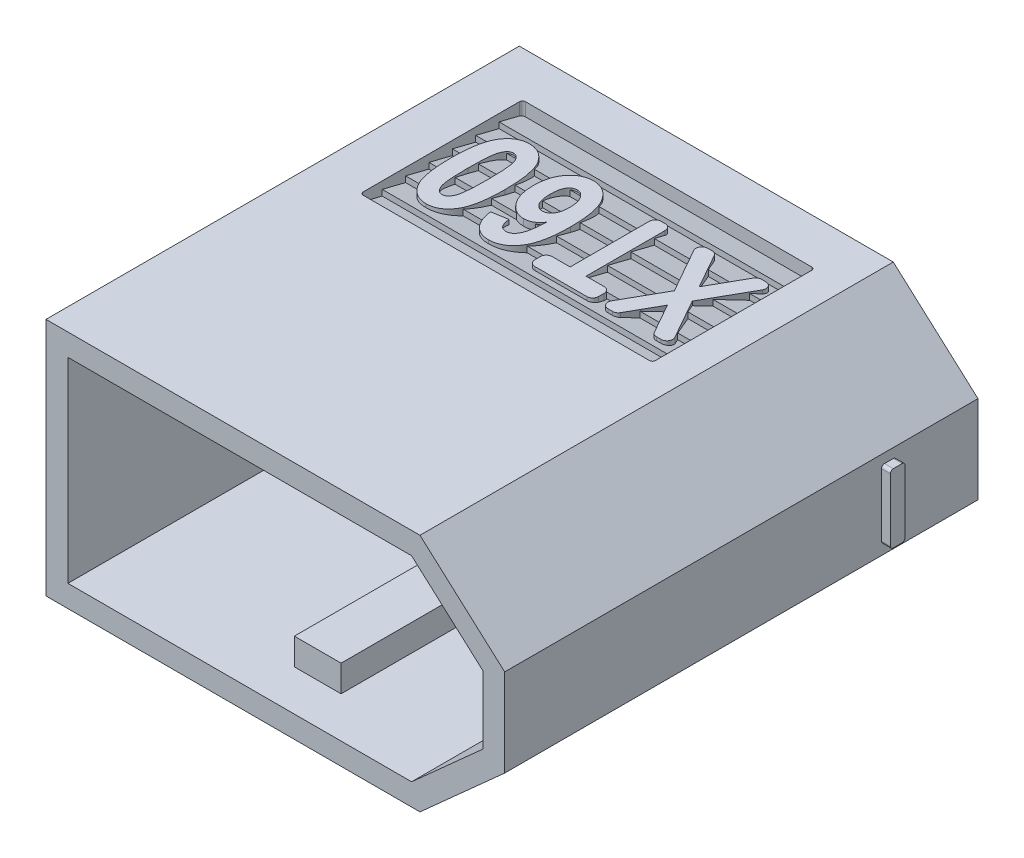
SolidWorks part; units mm, degrees
material "Nylon 101"
ref_plane "Plano frontal" through (0, 0, 0) normal (0, 0, 1) x (1, 0, 0)
ref_plane "Plano superior" through (0, 0, 0) normal (0, 1, 0) x (1, 0, 0)
ref_plane "Plano direito" through (0, 0, 0) normal (1, 0, 0) x (0, 0, -1)
sketch "Esboço1" plane through (0, 0, 0) normal (0, 0, 1) x (1, 0, 0)
  line L0 (0, 0) -> (12.8, 0)
  line L1 (12.8, 0) -> (15.7, 2.6)
  line L2 (15.7, 2.6) -> (15.7, 5.6)
  line L3 (15.7, 5.6) -> (12.8, 8.2)
  line L4 (12.8, 8.2) -> (0, 8.2)
  line L5 (0, 8.2) -> (0, 0)
  dimension "D1" = 12.8
  dimension "D2" = 3
  dimension "D3" = 15.7
  dimension "D4" = 8.2
extrude "Ressalto-extrusão1" add sketch "Esboço1" along normal blind 16.2
sketch "Esboço2" plane through (0, 0, 16.2) normal (0, 0, 1) x (1, 0, 0)
  line L0 (0.75, 7.45) -> (0.75, 0.75)
  line L1 (0.75, 0.75) -> (12.513, 0.75)
  line L2 (12.513, 0.75) -> (14.95, 2.9349)
  line L3 (14.95, 2.9349) -> (14.95, 5.2651)
  line L4 (14.95, 5.2651) -> (12.513, 7.45)
  line L5 (12.513, 7.45) -> (0.75, 7.45)
  line L6 (0, 8.2) -> (0, 0)
  line L7 (0, 0) -> (12.8, 0)
  line L8 (12.8, 0) -> (15.7, 2.6)
  line L9 (15.7, 2.6) -> (15.7, 5.6)
  line L10 (15.7, 5.6) -> (12.8, 8.2)
  line L11 (12.8, 8.2) -> (0, 8.2)
  line L12 (0, 8.2) -> (0, 0) construction
  line L13 (0, 0) -> (12.8, 0) construction
  line L14 (12.8, 0) -> (15.7, 2.6) construction
  line L15 (15.7, 2.6) -> (15.7, 5.6) construction
  line L16 (15.7, 5.6) -> (12.8, 8.2) construction
  line L17 (12.8, 8.2) -> (0, 8.2) construction
  dimension "D1" = 0
  dimension "D2" = 0.75
extrude "Corte-extrusão1" cut sketch "Esboço2" against normal blind 9.4
sketch "Esboço3" plane through (0, 0, 6.8) normal (0, 0, 1) x (1, 0, 0)
  line L1 (7.1, 1.66) -> (8.7, 1.66)
  line L2 (7.1, 1.66) -> (7.1, 0.75)
  line L3 (7.1, 0.75) -> (8.7, 0.75)
  line L4 (8.7, 1.66) -> (8.7, 0.75)
  line L7 (0.75, 0.75) -> (12.513, 0.75) construction
  line L8 (0, 0) -> (12.8, 0) construction
  line L9 (0, 8.2) -> (0, 0) construction
  dimension "D1" = 1.6
  dimension "D2" = 1.66
  dimension "D3" = 8.7
extrude "Ressalto-extrusão2" add sketch "Esboço3" along normal blind 8
sketch "Esboço4" plane through (0, 0, 6.8) normal (0, 0, 1) x (1, 0, 0)
  line L0 (12.513, 7.45) -> (0.75, 7.45) construction
  line L1 (8.7, 1.75) -> (7.1, 1.75)
  line L2 (8.7, 1.75) -> (8.7, 6.45)
  line L3 (8.7, 6.45) -> (7.1, 6.45)
  line L4 (7.1, 1.75) -> (7.1, 6.45)
  line L5 (0.75, 0.75) -> (7.1, 0.75) construction
  line L7 (7.1, 1.66) -> (7.1, 0.75) construction
  line L8 (8.7, 0.75) -> (8.7, 1.66) construction
  dimension "D1" = 1
  dimension "D2" = 1
extrude "Corte-extrusão2" cut sketch "Esboço4" against normal blind 1.5
sketch "Esboço5" plane through (0, 0, 0) normal (0, 0, -1) x (-1, 0, 0)
  line L0 (-15.7, 2.6) -> (-15.7, 5.6) construction
  line L3 (0, 8.2) -> (0, 0) construction
  circle A0 centre (-11.35, 4.1) radius 3
  circle A1 centre (-4.25, 4.1) radius 3
  point P6 (-15.7, 4.1)
  point P9 (-15.7, 4.1)
  dimension "D1" = 6
  dimension "D3" = 4.25
  dimension "D2" = 4.35
extrude "Corte-extrusão3" cut sketch "Esboço5" against normal blind 2
sketch "Esboço6" plane through (0, 0, 2) normal (0, 0, -1) x (-1, 0, 0)
  line L0 (-15.7, 2.6) -> (-15.7, 5.6) construction
  line L3 (0, 8.2) -> (0, 0) construction
  circle A0 centre (-11.35, 4.1) radius 2.15
  circle A2 centre (-4.25, 4.1) radius 2.15
  point P4 (-15.7, 4.1)
  dimension "D1" = 4.3
  dimension "D2" = 6.5
  dimension "D3" = 6.4
extrude "Corte-extrusão4" cut sketch "Esboço6" against normal through all
sketch "Esboço7" plane through (0, 0, 0) normal (-1, 0, 0) x (0, 0, 1)
  line L0 (2.8, 4.35) -> (2.05, 4.35)
  line L1 (4.25, 4.35) -> (3.5, 4.35)
  line L2 (4.35, 4.25) -> (4.35, 3.95)
  line L3 (4.25, 3.85) -> (3.5, 3.85)
  line L4 (1.95, 4.25) -> (1.95, 3.95)
  line L5 (3.3, 5.3) -> (3, 5.3)
  line L6 (3.4, 5.2) -> (3.4, 4.45)
  line L7 (3.3, 2.9) -> (3, 2.9)
  line L8 (2.9, 5.2) -> (2.9, 4.45)
  line L9 (2.8, 3.85) -> (2.05, 3.85)
  line L10 (3.4, 3.75) -> (3.4, 3)
  line L11 (2.9, 3.75) -> (2.9, 3)
  line L12 (0, 8.2) -> (0, 0) construction
  arc A0 (3, 2.9) -> (2.9, 3) centre (3, 3) cw
  arc A1 (3.3, 5.3) -> (3.4, 5.2) centre (3.3, 5.2) cw
  arc A2 (3, 5.3) -> (2.9, 5.2) centre (3, 5.2) ccw
  arc A3 (2.05, 4.35) -> (1.95, 4.25) centre (2.05, 4.25) ccw
  arc A4 (2.05, 3.85) -> (1.95, 3.95) centre (2.05, 3.95) cw
  arc A5 (2.8, 3.85) -> (2.9, 3.75) centre (2.8, 3.75) cw
  arc A6 (2.8, 4.35) -> (2.9, 4.45) centre (2.8, 4.45) ccw
  arc A7 (3.5, 3.85) -> (3.4, 3.75) centre (3.5, 3.75) ccw
  arc A8 (3.4, 3) -> (3.3, 2.9) centre (3.3, 3) cw
  arc A9 (4.35, 3.95) -> (4.25, 3.85) centre (4.25, 3.95) cw
  arc A10 (4.25, 4.35) -> (4.35, 4.25) centre (4.25, 4.25) cw
  arc A11 (3.5, 4.35) -> (3.4, 4.45) centre (3.5, 4.45) cw
  point P12 (1.95, 4.1)
  point P15 (0, 4.1)
  point P28 (2.9, 3.85)
  point P33 (3.4, 3.85)
  point P38 (4.35, 3.85)
  point P41 (4.35, 4.35)
  dimension "D4" = 0.1
  dimension "D1" = 2.4
  dimension "D2" = 0.5
  dimension "D3" = 4.35
extrude "Ressalto-extrusão3" add sketch "Esboço7" along normal blind 0.3
sketch "Esboço8" plane through (15.7, 0, 0) normal (1, 0, 0) x (0, 0, -1)
  line L0 (0, 2.6) -> (0, 5.6) construction
  line L1 (-3.2, 2.925) -> (-2.9, 2.925)
  line L2 (-3.3, 3.025) -> (-3.3, 5.175)
  line L3 (-3.2, 5.275) -> (-2.9, 5.275)
  line L4 (-2.8, 3.025) -> (-2.8, 5.175)
  arc A0 (-3.3, 5.175) -> (-3.2, 5.275) centre (-3.2, 5.175) cw
  arc A1 (-2.9, 5.275) -> (-2.8, 5.175) centre (-2.9, 5.175) cw
  arc A2 (-3.2, 2.925) -> (-3.3, 3.025) centre (-3.2, 3.025) cw
  arc A3 (-2.9, 2.925) -> (-2.8, 3.025) centre (-2.9, 3.025) ccw
  point P4 (-2.8, 4.1)
  point P7 (0, 4.1)
  point P10 (-3.3, 5.275)
  point P13 (-2.8, 5.275)
  point P18 (-2.8, 2.925)
  dimension "D4" = 0.1
  dimension "D1" = 2.35
  dimension "D2" = 0.5
  dimension "D3" = 3.3
extrude "Ressalto-extrusão4" add sketch "Esboço8" along normal blind 0.3
sketch "Esboço9" plane through (0, 0, 0) normal (0, -1, 0) x (1, 0, 0)
  line L0 (12.8, 16.2) -> (12.8, 0) construction
  line L1 (1.75, 7.0931) -> (11.55, 7.0931)
  line L2 (1.65, 6.9931) -> (1.65, 1.6431)
  line L3 (1.75, 1.5431) -> (11.55, 1.5431)
  line L4 (11.65, 6.9931) -> (11.65, 1.6431)
  arc A0 (1.65, 1.6431) -> (1.75, 1.5431) centre (1.75, 1.6431) ccw
  arc A1 (11.55, 1.5431) -> (11.65, 1.6431) centre (11.55, 1.6431) ccw
  arc A2 (11.55, 7.0931) -> (11.65, 6.9931) centre (11.55, 6.9931) cw
  arc A3 (1.75, 7.0931) -> (1.65, 6.9931) centre (1.75, 6.9931) ccw
  dimension "D1" = 0.1
  dimension "D2" = 1.15
  dimension "D3" = 10
  dimension "D4" = 5.55
extrude "Corte-extrusão5" cut sketch "Esboço9" against normal blind 0.75
sketch "Esboço10" plane through (1.65, 0, 0) normal (1, 0, 0) x (0, 0, -1)
  line L0 (-6.8, 0.75) -> (-1.6431, 0.75) construction
  line L1 (-1.5431, 0.75) -> (-1.5431, 0) construction
  line L2 (-3.1431, 0.25) -> (-2.3431, 0.45)
  line L3 (-2.3431, 0.45) -> (-2.3431, 0.25)
  line L5 (-3.1431, 0.45) -> (-3.1431, 0.25)
  line L6 (-2.3431, 0.45) -> (-2.3431, 0.25)
  line L7 (-3.9431, 0.25) -> (-3.1431, 0.45)
  line L8 (-3.9431, 0.45) -> (-3.9431, 0.25)
  line L9 (-4.7431, 0.25) -> (-3.9431, 0.45)
  line L10 (-4.7431, 0.45) -> (-4.7431, 0.25)
  line L11 (-5.5431, 0.25) -> (-4.7431, 0.45)
  line L12 (-5.5431, 0.45) -> (-5.5431, 0.25)
  line L13 (-6.3431, 0.25) -> (-5.5431, 0.45)
  line L14 (-6.3431, 0.45) -> (-6.3431, 0.25)
  line L15 (-7.1431, 0.25) -> (-6.3431, 0.45)
  line L16 (-7.1431, 0.45) -> (-7.1431, 0.25)
  line L17 (-7.1431, 0.45) -> (-7.1431, 0.75)
  line L19 (-2.3431, 0.25) -> (-1.5431, 0.45)
  line L20 (-7.1431, 0.75) -> (-1.5431, 0.75)
  line L21 (-1.5431, 0.45) -> (-1.5431, 0.75)
  line L31 (-2.3431, 0.25) -> (-1.5431, 0.45)
  dimension "D1" = 0.8
  dimension "D2" = 0.2
  dimension "D3" = 0.3
  dimension "D4" = 7
extrude "Ressalto-extrusão7" add sketch "Esboço10" along normal up to surface (10 mm away) up to face at (11.65, 0.45, 4.8145)
ref_plane "Plano1" through (0, 4.1, 0) normal (0, 1, 0) x (1, 0, 0)
mirror "Espelhar1" about plane through (0, 4.1, 0) normal (0, 1, 0) of "Corte-extrusão5", "Ressalto-extrusão7"
ref_plane "Plano2" through (0, 0.5, 0) normal (0, -1, 0) x (-1, 0, 0)
sketch "Esboço11" plane through (0, 0.5, 0) normal (0, -1, 0) x (-1, 0, 0)
  line L1 (-2.131, -7.0931) -> (-2.131, -1.5431) construction
  line L2 (-11.55, -7.0931) -> (-1.75, -7.0931) construction
  line L3 (-11.55, -1.5431) -> (-1.75, -1.5431) construction
  line L4 (-0.85, -6.1831) -> (-0.85, -2.4531) construction
  line L5 (-0.85, -2.4531) -> (-11.65, -2.4531) construction
  line L8 (-11.65, -3.1431) -> (-11.65, -2.3431) construction
  line L10 (-1.65, -6.9931) -> (-1.65, -1.6431) construction
  text T0 "<b><i>TGY</i></b>" font "Calibri" height in points 14
  point P8 (-0.85, -4.3181)
  point P9 (-2.131, -4.3181)
  dimension "D2" = 0.8
  dimension "D1" = 3.73
extrude "Ressalto-extrusão8" add sketch "Esboço11" along normal blind 0.3
ref_plane "Plano3" through (0, 7.7, 0) normal (0, 1, 0) x (1, 0, 0)
sketch "Esboço12" plane through (0, 7.7, 0) normal (0, 1, 0) x (1, 0, 0)
  line L0 (11.0942, -7.0931) -> (11.0942, -1.5431) construction
  line L1 (11.55, -7.0931) -> (1.75, -7.0931) construction
  line L3 (11.3535, -6.0681) -> (11.3535, -2.5681) construction
  line L6 (11.3535, -2.5681) -> (1.9746, -2.5681) construction
  line L7 (11.185, -2.8665) -> (10.3201, -4.3984)
  line L8 (10.3201, -4.3984) -> (11.0942, -5.7698)
  line L9 (10.92, -6.0681) -> (10.7649, -6.0681)
  line L10 (10.5908, -5.9665) -> (10.0126, -4.9431)
  line L11 (10.0126, -4.9431) -> (9.435, -5.9664)
  line L12 (9.2609, -6.0681) -> (9.1051, -6.0681)
  line L13 (8.931, -5.7698) -> (9.705, -4.3984)
  line L14 (9.705, -4.3984) -> (8.8401, -2.8665)
  line L15 (9.0143, -2.5681) -> (9.1699, -2.5681)
  line L16 (9.3441, -2.6698) -> (10.0126, -3.8543)
  line L17 (10.0126, -3.8543) -> (10.6817, -2.6698)
  line L18 (10.8559, -2.5681) -> (11.0109, -2.5681)
  line L19 (7.7626, -2.7681) -> (7.7626, -5.4772)
  line L20 (7.7626, -5.4772) -> (8.3808, -5.4772)
  line L21 (8.5808, -5.6772) -> (8.5808, -5.8681)
  line L22 (8.3808, -6.0681) -> (6.5989, -6.0681)
  line L23 (6.3989, -5.8681) -> (6.3989, -5.6772)
  line L24 (6.5989, -5.4772) -> (7.2171, -5.4772)
  line L25 (7.2171, -5.4772) -> (7.2171, -2.7681)
  line L26 (7.4171, -2.5681) -> (7.5626, -2.5681)
  line L27 (4.2171, -5.2045) -> (4.7626, -5.1136)
  line L28 (11.55, -1.5431) -> (1.75, -1.5431) construction
  arc A0 (7.2171, -2.7681) -> (7.4171, -2.5681) centre (7.4171, -2.7681) cw
  arc A1 (7.7626, -2.7681) -> (7.5626, -2.5681) centre (7.5626, -2.7681) ccw
  arc A2 (6.3989, -5.6772) -> (6.5989, -5.4772) centre (6.5989, -5.6772) cw
  arc A3 (6.5989, -6.0681) -> (6.3989, -5.8681) centre (6.5989, -5.8681) cw
  arc A4 (8.5808, -5.8681) -> (8.3808, -6.0681) centre (8.3808, -5.8681) cw
  arc A5 (8.3808, -5.4772) -> (8.5808, -5.6772) centre (8.3808, -5.6772) cw
  arc A6 (11.185, -2.8665) -> (11.0109, -2.5681) centre (11.0109, -2.7681) ccw
  arc A7 (10.6817, -2.6698) -> (10.8559, -2.5681) centre (10.8559, -2.7681) cw
  arc A8 (9.1699, -2.5681) -> (9.3441, -2.6698) centre (9.1699, -2.7681) cw
  arc A9 (8.8401, -2.8665) -> (9.0143, -2.5681) centre (9.0143, -2.7681) cw
  arc A10 (9.1051, -6.0681) -> (8.931, -5.7698) centre (9.1051, -5.8681) cw
  arc A11 (9.435, -5.9664) -> (9.2609, -6.0681) centre (9.2609, -5.8681) cw
  arc A12 (10.7649, -6.0681) -> (10.5908, -5.9665) centre (10.7649, -5.8681) cw
  arc A13 (11.0942, -5.7698) -> (10.92, -6.0681) centre (10.92, -5.8681) cw
  spline S0 degree 3 poles (4.7626, -5.1136) (4.7682, -5.1739) (4.7813, -5.2594) (4.8192, -5.3612) (4.8534, -5.4198) (4.8944, -5.4666) (4.9618, -5.511) (5.022, -5.5233) (5.0623, -5.5227) knots 0 0 0 0 0.323351 0.457032 0.575726 0.682828 0.785622 1 1 1 1
  spline S1 degree 3 poles (5.0623, -5.5227) (5.09, -5.5233) (5.1312, -5.5165) (5.1832, -5.4965) (5.2201, -5.4751) (5.2548, -5.4474) (5.2873, -5.4137) (5.3188, -5.3744) (5.3485, -5.328) (5.3759, -5.2719) (5.4005, -5.2044) (5.4208, -5.1242) (5.4414, -5.0325) (5.4567, -4.9277) (5.4769, -4.7639) (5.4853, -4.6343) (5.4898, -4.544) knots 0 0 0 0 0.071106 0.106432 0.143035 0.180361 0.220458 0.263402 0.309744 0.362096 0.423824 0.494518 0.575001 0.665718 0.767055 1 1 1 1
  spline S2 degree 3 poles (5.4898, -4.544) (5.4583, -4.5903) (5.407, -4.6546) (5.3276, -4.7255) (5.2671, -4.7681) (5.2028, -4.8002) (5.1126, -4.8326) (5.0401, -4.8399) (4.992, -4.8409) knots 0 0 0 0 0.277998 0.405178 0.526602 0.643637 0.760549 1 1 1 1
  spline S3 degree 3 poles (4.992, -4.8409) (4.9384, -4.84) (4.8576, -4.8324) (4.7559, -4.798) (4.6823, -4.7636) (4.6106, -4.7202) (4.5426, -4.6656) (4.4769, -4.602) (4.4148, -4.529) (4.3577, -4.4481) (4.3074, -4.36) (4.2661, -4.2652) (4.2305, -4.1646) (4.205, -4.0571) (4.1787, -3.9021) (4.1709, -3.7817) (4.1717, -3.6995) knots 0 0 0 0 0.103373 0.154207 0.205955 0.259297 0.315055 0.373347 0.435039 0.499095 0.563542 0.6298 0.697776 0.768574 0.842016 1 1 1 1
  spline S4 degree 3 poles (4.1717, -3.6995) (4.1719, -3.6124) (4.1791, -3.4851) (4.2059, -3.3214) (4.2344, -3.2096) (4.2696, -3.1044) (4.3147, -3.0075) (4.3663, -2.9169) (4.427, -2.8357) (4.4929, -2.7625) (4.5632, -2.698) (4.638, -2.6441) (4.7161, -2.5992) (4.7984, -2.5649) (4.9149, -2.5326) (5.0059, -2.5223) (5.0673, -2.5227) knots 0 0 0 0 0.157847 0.230497 0.300424 0.366636 0.431332 0.493809 0.555163 0.614703 0.672107 0.727719 0.78152 0.834986 0.88891 1 1 1 1
  spline S5 degree 3 poles (5.0673, -2.5227) (5.1348, -2.5224) (5.235, -2.5352) (5.3621, -2.5775) (5.4516, -2.6225) (5.5367, -2.6804) (5.6167, -2.7511) (5.6923, -2.8344) (5.764, -2.9301) (5.8292, -3.0408) (5.8839, -3.1688) (5.9316, -3.3125) (5.969, -3.4733) (5.9997, -3.6502) (6.0283, -3.9192) (6.0353, -4.1298) (6.0353, -4.2755) knots 0 0 0 0 0.090693 0.134685 0.17953 0.224913 0.272738 0.32276 0.375986 0.433204 0.49507 0.562819 0.636478 0.716918 0.804031 1 1 1 1
  spline S6 degree 3 poles (6.0353, -4.2755) (6.0353, -4.4236) (6.0286, -4.6379) (5.9972, -4.9112) (5.9666, -5.0917) (5.9263, -5.2555) (5.8779, -5.4031) (5.8201, -5.5343) (5.7518, -5.6479) (5.6774, -5.7469) (5.5976, -5.8325) (5.5132, -5.906) (5.4224, -5.9645) (5.3276, -6.0115) (5.1918, -6.0556) (5.0843, -6.0686) (5.0119, -6.0681) knots 0 0 0 0 0.192658 0.278521 0.357597 0.430563 0.497753 0.559502 0.616537 0.669747 0.720292 0.768555 0.814847 0.860431 0.905809 1 1 1 1
  spline S7 degree 3 poles (5.0119, -6.0681) (4.9619, -6.0679) (4.888, -6.0616) (4.793, -6.0396) (4.7258, -6.0161) (4.6619, -5.9851) (4.6002, -5.9489) (4.5418, -5.9054) (4.4872, -5.8546) (4.4355, -5.7981) (4.3903, -5.7331) (4.3488, -5.6621) (4.3131, -5.5835) (4.2805, -5.4988) (4.2454, -5.3724) (4.226, -5.2732) (4.2171, -5.2045) knots 0 0 0 0 0.115543 0.170649 0.225187 0.279791 0.334526 0.390474 0.447811 0.50673 0.567186 0.630471 0.696846 0.766493 0.839959 1 1 1 1
  spline S8 degree 3 poles (5.4444, -3.7215) (5.4434, -3.6718) (5.4418, -3.5989) (5.429, -3.5058) (5.4165, -3.4425) (5.399, -3.3843) (5.3797, -3.33) (5.3555, -3.2808) (5.3274, -3.2367) (5.298, -3.1971) (5.2668, -3.1628) (5.2343, -3.1343) (5.2019, -3.1095) (5.1674, -3.0908) (5.1199, -3.0739) (5.0828, -3.0683) (5.058, -3.0681) knots 0 0 0 0 0.178482 0.260709 0.336948 0.409468 0.478213 0.543503 0.605673 0.665087 0.720356 0.771459 0.82001 0.866345 0.91145 1 1 1 1
  spline S9 degree 3 poles (5.058, -3.0681) (5.0113, -3.0673) (4.9398, -3.0858) (4.8626, -3.147) (4.82, -3.1972) (4.7904, -3.2464) (4.7705, -3.2897) (4.7544, -3.3389) (4.7402, -3.3931) (4.7296, -3.4532) (4.7205, -3.5442) (4.7163, -3.6154) (4.7171, -3.6647) knots 0 0 0 0 0.182718 0.277312 0.381921 0.439334 0.501577 0.568146 0.641921 0.72105 0.806868 1 1 1 1
  spline S10 degree 3 poles (4.7171, -3.6647) (4.717, -3.7159) (4.7193, -3.7901) (4.7313, -3.8847) (4.7423, -3.9476) (4.7573, -4.005) (4.7747, -4.0573) (4.7959, -4.1039) (4.8285, -4.1562) (4.8734, -4.2114) (4.9574, -4.2751) (5.0328, -4.2967) (5.0829, -4.2954) knots 0 0 0 0 0.189208 0.273855 0.352112 0.425324 0.492836 0.555472 0.613995 0.720194 0.816437 1 1 1 1
  spline S11 degree 3 poles (5.0829, -4.2954) (5.1315, -4.2955) (5.2057, -4.2763) (5.2877, -4.2147) (5.333, -4.163) (5.3652, -4.1135) (5.3866, -4.0705) (5.4042, -4.0231) (5.4192, -3.9714) (5.4302, -3.915) (5.4422, -3.8316) (5.4445, -3.7663) (5.4444, -3.7215) knots 0 0 0 0 0.192976 0.293261 0.403879 0.464413 0.527516 0.593907 0.665362 0.741186 0.821937 1 1 1 1
  spline S12 degree 3 poles (2.8776, -6.0681) (2.8107, -6.0678) (2.7113, -6.0563) (2.586, -6.0147) (2.4983, -5.9711) (2.4159, -5.915) (2.3386, -5.8466) (2.2662, -5.766) (2.1985, -5.6725) (2.1376, -5.5631) (2.0855, -5.436) (2.0419, -5.2906) (2.0063, -5.1269) (1.978, -4.9448) (1.9513, -4.6654) (1.9446, -4.4461) (1.9444, -4.294) knots 0 0 0 0 0.08972 0.132871 0.17644 0.220536 0.26618 0.314488 0.365396 0.420661 0.481834 0.549191 0.623951 0.706175 0.796104 1 1 1 1
  spline S13 degree 3 poles (1.9444, -4.294) (1.9446, -4.1424) (1.9512, -3.9238) (1.9781, -3.6451) (2.0061, -3.4634) (2.0421, -3.2998) (2.0852, -3.1545) (2.1378, -3.0275) (2.1984, -2.9183) (2.2663, -2.8251) (2.3378, -2.744) (2.4152, -2.6758) (2.4975, -2.6199) (2.5847, -2.5759) (2.7095, -2.5348) (2.8083, -2.5226) (2.8748, -2.5227) knots 0 0 0 0 0.203744 0.29357 0.37599 0.450617 0.518438 0.579462 0.634858 0.685888 0.734097 0.77985 0.824051 0.867439 0.910692 1 1 1 1
  spline S14 degree 3 poles (2.8748, -2.5227) (2.9415, -2.5237) (3.0413, -2.5333) (3.1662, -2.5756) (3.2543, -2.618) (3.3363, -2.6745) (3.4139, -2.742) (3.4862, -2.8219) (3.5413, -2.8978) (3.5827, -2.965) (3.6116, -3.0212) (3.6385, -3.082) (3.6644, -3.1471) (3.6866, -3.2179) (3.708, -3.2929) (3.7271, -3.3725) (3.744, -3.4569) (3.76, -3.5458) (3.7721, -3.64) (3.784, -3.7384) (3.792, -3.842) (3.7994, -3.9499) (3.8057, -4.1036) (3.809, -4.221) (3.808, -4.3011) knots 0 0 0 0 0.089418 0.132451 0.175762 0.219738 0.26505 0.312991 0.363505 0.390209 0.418376 0.447842 0.479108 0.512034 0.546898 0.583358 0.621467 0.661946 0.704107 0.748387 0.794432 0.842956 0.893008 1 1 1 1
  spline S15 degree 3 poles (3.808, -4.3011) (3.8078, -4.4522) (3.8011, -4.6701) (3.7744, -4.9476) (3.7461, -5.1285) (3.7104, -5.2915) (3.6671, -5.4365) (3.6147, -5.5633) (3.554, -5.6725) (3.4861, -5.7657) (3.4146, -5.8468) (3.3372, -5.915) (3.255, -5.9709) (3.1677, -6.0149) (3.0429, -6.056) (2.9441, -6.0682) (2.8776, -6.0681) knots 0 0 0 0 0.203492 0.293171 0.375116 0.449884 0.517528 0.578668 0.634169 0.685295 0.733595 0.779434 0.823719 0.867188 0.910523 1 1 1 1
  spline S16 degree 3 poles (2.8762, -5.5227) (2.9014, -5.5225) (2.9391, -5.5157) (2.9853, -5.4936) (3.0177, -5.4696) (3.0472, -5.4386) (3.0753, -5.4017) (3.1015, -5.3582) (3.1264, -5.3061) (3.1493, -5.2412) (3.1662, -5.1592) (3.1829, -5.0598) (3.1947, -4.9418) (3.2056, -4.806) (3.2148, -4.5879) (3.2172, -4.4152) (3.2171, -4.294) knots 0 0 0 0 0.054972 0.082543 0.111449 0.142586 0.175843 0.2128 0.253578 0.301908 0.362982 0.436475 0.522453 0.622213 0.734739 1 1 1 1
  spline S17 degree 3 poles (3.2171, -4.294) (3.2172, -4.173) (3.2148, -4.0006) (3.2056, -3.7827) (3.1946, -3.6468) (3.1829, -3.5291) (3.1662, -3.4301) (3.1492, -3.3487) (3.1266, -3.2841) (3.1014, -3.2324) (3.0751, -3.189) (3.0477, -3.1515) (3.0174, -3.1212) (2.9854, -3.0972) (2.9391, -3.0752) (2.9014, -3.0683) (2.8762, -3.0681) knots 0 0 0 0 0.265262 0.378009 0.477964 0.564111 0.637236 0.697923 0.746348 0.786738 0.823768 0.857504 0.888332 0.917295 0.944921 1 1 1 1
  spline S18 degree 3 poles (2.8762, -3.0681) (2.8509, -3.0683) (2.8128, -3.0749) (2.7663, -3.0974) (2.7333, -3.1209) (2.7037, -3.1525) (2.675, -3.1892) (2.6497, -3.2336) (2.6244, -3.2852) (2.6028, -3.3503) (2.5854, -3.4315) (2.5689, -3.5305) (2.5569, -3.648) (2.5471, -3.7837) (2.5374, -4.001) (2.5353, -4.1732) (2.5353, -4.294) knots 0 0 0 0 0.055564 0.083174 0.11254 0.143719 0.17775 0.214492 0.255326 0.303553 0.364206 0.437289 0.523386 0.622727 0.735409 1 1 1 1
  spline S19 degree 3 poles (2.5353, -4.294) (2.5354, -4.4152) (2.5374, -4.5879) (2.5471, -4.8059) (2.5568, -4.9419) (2.5689, -5.0598) (2.5854, -5.1593) (2.6027, -5.241) (2.6243, -5.3063) (2.6498, -5.3579) (2.6747, -5.4022) (2.7039, -5.4384) (2.7333, -5.4699) (2.7663, -5.4934) (2.8128, -5.5158) (2.8509, -5.5225) (2.8762, -5.5227) knots 0 0 0 0 0.265055 0.377494 0.477137 0.563048 0.636484 0.697511 0.745634 0.78638 0.823042 0.856591 0.887703 0.917006 0.944556 1 1 1 1
  point P7 (11.0942, -4.3181)
  point P10 (11.3535, -4.3181)
  dimension "D2" = 0.2
  dimension "D1" = 3.5
extrude "Ressalto-extrusão9" add sketch "Esboço12" along normal blind 0.3
